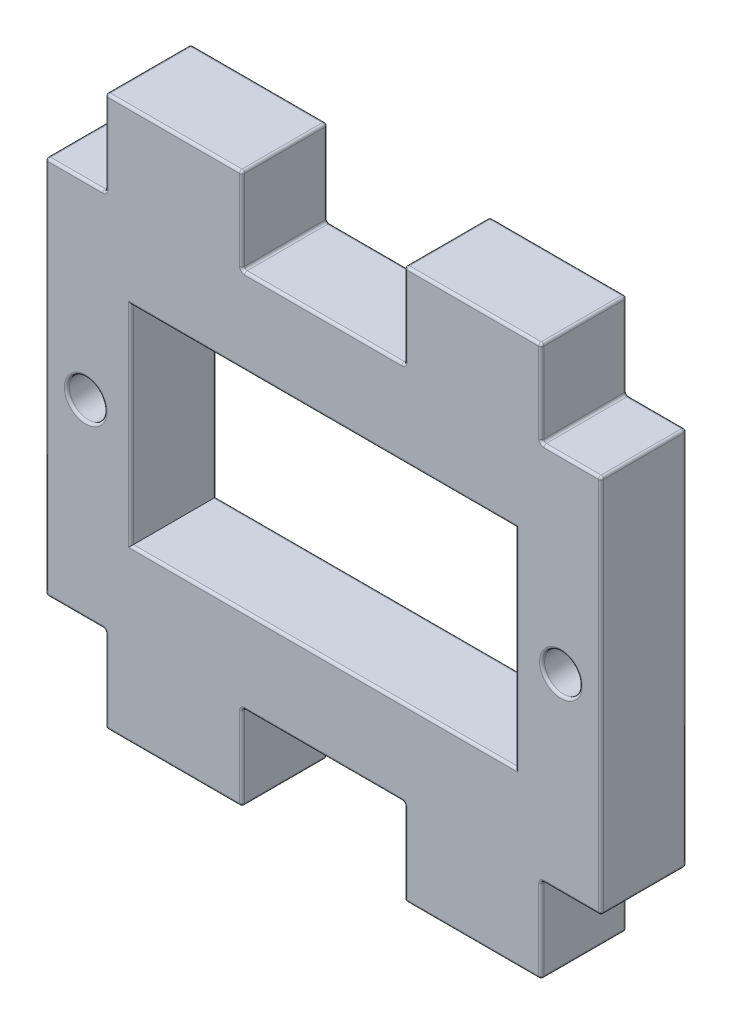
SolidWorks part; units mm, degrees
ref_plane "Płaszczyzna przednia" through (0, 0, 0) normal (0, 0, 1) x (1, 0, 0)
ref_plane "Płaszczyzna górna" through (0, 0, 0) normal (0, 1, 0) x (1, 0, 0)
ref_plane "Płaszczyzna prawa" through (0, 0, 0) normal (1, 0, 0) x (0, 0, -1)
sketch "Szkic1" plane through (0, 0, 0) normal (0, 0, 1) x (1, 0, 0)
  line L0 (-16.25, 11.1) -> (16.25, 11.1)
  line L1 (-11.25, -6.1) -> (11.25, -6.1)
  line L2 (-11.25, -6.1) -> (-11.25, 6.1)
  line L3 (-11.25, 6.1) -> (11.25, 6.1)
  line L4 (11.25, -6.1) -> (11.25, 6.1)
  line L5 (-11.25, -6.1) -> (11.25, 6.1) construction
  line L6 (-11.25, 6.1) -> (11.25, -6.1) construction
  line L7 (16.25, -11.1) -> (16.25, 11.1)
  line L8 (-16.25, -11.1) -> (16.25, -11.1)
  line L9 (-16.25, -11.1) -> (-16.25, 11.1)
  line L10 (0, 0) -> (0, 6.1) construction
  line L11 (-12.75, 11.1) -> (-4.75, 11.1)
  line L12 (-12.75, 11.1) -> (-12.75, 16.1)
  line L13 (-12.75, 16.1) -> (-4.75, 16.1)
  line L14 (-4.75, 11.1) -> (-4.75, 16.1)
  line L15 (0, 0) -> (-16.25, 0) construction
  line L16 (4.75, 11.1) -> (4.75, 16.1)
  line L17 (12.75, 16.1) -> (4.75, 16.1)
  line L18 (12.75, 11.1) -> (12.75, 16.1)
  line L19 (12.75, -11.1) -> (12.75, -16.1)
  line L20 (12.75, -16.1) -> (4.75, -16.1)
  line L21 (4.75, -11.1) -> (4.75, -16.1)
  line L22 (-4.75, -11.1) -> (-4.75, -16.1)
  line L23 (-12.75, -16.1) -> (-4.75, -16.1)
  line L24 (-12.75, -11.1) -> (-12.75, -16.1)
  circle A0 centre (-13.9, 0) radius 1.1
  circle A1 centre (13.9, 0) radius 1.1
  point P0 (0, 0)
  dimension "D7" = 2.2
  dimension "D1" = 12.2
  dimension "D2" = 22.5
  dimension "D4" = 3.5
  dimension "D5" = 5
  dimension "D6" = 8
  dimension "D8" = 2.65
  dimension "D3" = 5
extrude "Dodanie-wyciągnięcie1" add sketch "Szkic1" along normal mid plane 5 contours L9 L8 L7 L0 L4 L1 L2 L3 A0 A1 | L8 L24 L23 L22 | L8 L21 L20 L19 | L0 L18 L17 L16 | L0 L14 L13 L12
fillet "Zaokrąglenie1" radius 0.15 60 edges at (-12.75, 16.1, 0) (-8.75, 16.1, -2.5) (-8.75, 16.1, 2.5) (-12.75, 13.6, -2.5) (-12.75, 13.6, 2.5) (-4.75, 16.1, 0) (-12.75, 11.1, 0) (-4.75, 13.6, -2.5) (-4.75, 13.6, 2.5) (-14.5, 11.1, 2.5) (-14.5, 11.1, -2.5) (-4.75, 11.1, 0) (-16.25, 11.1, 0) (0, 11.1, -2.5) (0, 11.1, 2.5) (-16.25, 0, -2.5) (-16.25, 0, 2.5) (4.75, 11.1, 0) (-16.25, -11.1, 0) (4.75, 13.6, -2.5) (4.75, 13.6, 2.5) (-14.5, -11.1, 2.5) (-14.5, -11.1, -2.5) (4.75, 16.1, 0) (-12.75, -11.1, 0) (8.75, 16.1, -2.5) (8.75, 16.1, 2.5) (-12.75, -13.6, -2.5) (-12.75, -13.6, 2.5) (12.75, 16.1, 0) (-12.75, -16.1, 0) (12.75, 13.6, -2.5) (12.75, 13.6, 2.5) (-8.75, -16.1, -2.5) (-8.75, -16.1, 2.5) (12.75, 11.1, 0) (-4.75, -16.1, 0) (14.5, 11.1, 2.5) (14.5, 11.1, -2.5) (-4.75, -13.6, -2.5) (-4.75, -13.6, 2.5) (16.25, 11.1, 0) (-4.75, -11.1, 0) (16.25, 0, -2.5) (16.25, 0, 2.5) (0, -11.1, 2.5) (0, -11.1, -2.5) (16.25, -11.1, 0) (4.75, -11.1, 0) (14.5, -11.1, 2.5) (14.5, -11.1, -2.5) (4.75, -13.6, -2.5) (4.75, -13.6, 2.5) (12.75, -11.1, 0) (4.75, -16.1, 0) (12.75, -13.6, -2.5) (12.75, -13.6, 2.5) (8.75, -16.1, -2.5) (8.75, -16.1, 2.5) (12.75, -16.1, 0)
fillet "Zaokrąglenie2" radius 0.15 12 edges at (15, 0, 2.5) (15, 0, -2.5) (-12.8, 0, 2.5) (-12.8, 0, -2.5) (0, -6.1, -2.5) (0, -6.1, 2.5) (-11.25, 0, -2.5) (-11.25, 0, 2.5) (0, 6.1, -2.5) (0, 6.1, 2.5) (11.25, 0, -2.5) (11.25, 0, 2.5)
